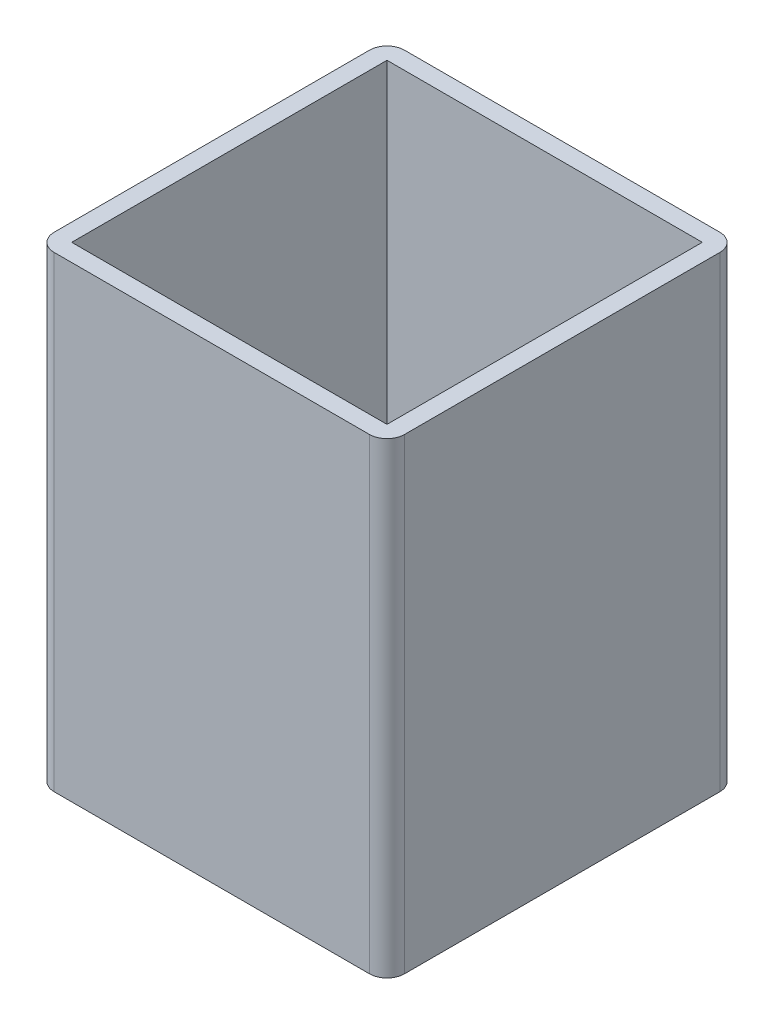
SolidWorks part; units mm, degrees
ref_plane "Front Plane" through (0, 0, 0) normal (0, 0, 1) x (1, 0, 0)
ref_plane "Top Plane" through (0, 0, 0) normal (0, 1, 0) x (1, 0, 0)
ref_plane "Right Plane" through (0, 0, 0) normal (1, 0, 0) x (0, 0, -1)
sketch "Sketch1" plane through (0, 0, 0) normal (0, 1, 0) x (1, 0, 0)
  line L0 (3, 57) -> (57, 57)
  line L1 (0, 0) -> (60, 0)
  line L2 (0, 0) -> (0, 60)
  line L3 (0, 60) -> (60, 60)
  line L4 (60, 0) -> (60, 60)
  line L5 (57, 3) -> (57, 57)
  line L6 (3, 3) -> (57, 3)
  line L7 (3, 3) -> (3, 57)
  dimension "D1" = 60
  dimension "D2" = 3
extrude "Boss-Extrude1" add sketch "Sketch1" along normal blind 80
fillet "Fillet2" radius 3 4 edges at (0, 40, -60) (0, 40, 0) (60, 40, 0) (60, 40, -60)
